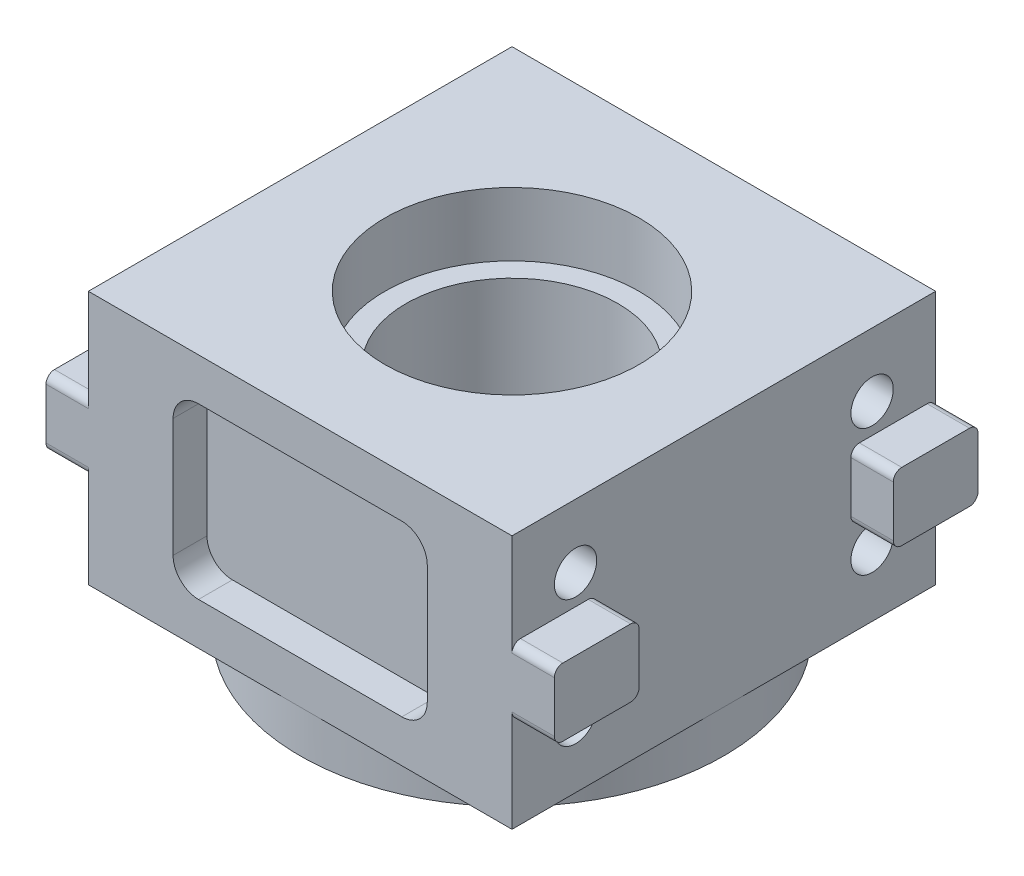
SolidWorks part; units mm, degrees
material "6061-T6 (SS)"
ref_plane "Front Plane" through (0, 0, 0) normal (0, 0, 1) x (1, 0, 0)
ref_plane "Top Plane" through (0, 0, 0) normal (0, 1, 0) x (1, 0, 0)
ref_plane "Right Plane" through (0, 0, 0) normal (1, 0, 0) x (0, 0, -1)
sketch "Sketch1" plane through (0, 0, 0) normal (0, 1, 0) x (1, 0, 0)
  line L1 (63.5, 63.5) -> (-63.5, 63.5)
  line L2 (63.5, 63.5) -> (63.5, -63.5)
  line L3 (63.5, -63.5) -> (-63.5, -63.5)
  line L4 (-63.5, 63.5) -> (-63.5, -63.5)
  line L5 (63.5, 63.5) -> (-63.5, -63.5) construction
  line L6 (63.5, -63.5) -> (-63.5, 63.5) construction
  circle A0 centre (0, 0) radius 38.1
  point P0 (0, 0)
  dimension "D3" = 76.2
  dimension "D1" = 127
  dimension "D2" = 127
extrude "Boss-Extrude1" add sketch "Sketch1" along normal blind 76.2
sketch "Sketch2" plane through (-63.5, 0, 0) normal (-1, 0, 0) x (0, 0, 1)
  line L0 (0, 76.2) -> (0, 0)
  line L1 (-63.5, 76.2) -> (63.5, 76.2) construction
  line L2 (-63.5, 0) -> (63.5, 0) construction
  line L3 (63.5, 76.2) -> (63.5, 0) construction
  line L4 (44.45, 19.05) -> (-44.45, 19.05)
  line L5 (44.45, 19.05) -> (44.45, 57.15)
  line L6 (44.45, 57.15) -> (-44.45, 57.15)
  line L7 (-44.45, 19.05) -> (-44.45, 57.15)
  line L8 (44.45, 19.05) -> (-44.45, 57.15) construction
  line L9 (44.45, 57.15) -> (-44.45, 19.05) construction
  circle A0 centre (-44.45, 57.15) radius 6.35
  circle A1 centre (-44.45, 19.05) radius 6.35
  circle A2 centre (44.45, 57.15) radius 6.35
  circle A3 centre (44.45, 19.05) radius 6.35
  point P6 (0, 38.1)
  dimension "D2" = 12.7
  dimension "D3" = 19.05
  dimension "D4" = 19.05
extrude "Cut-Extrude1" cut sketch "Sketch2" against normal blind 25.4 contours A2 | A0 | A1 | A3
mirror "Mirror1" about plane through (0, 0, 0) normal (1, 0, 0) of "Cut-Extrude1"
sketch "Sketch3" plane through (0, 0, 0) normal (0, -1, 0) x (1, 0, 0)
  circle A0 centre (0, 0) radius 38.1 construction
  circle A1 centre (0, 0) radius 38.1
  circle A2 centre (0, 0) radius 63.5
  dimension "D1" = 127
extrude "Boss-Extrude2" add sketch "Sketch3" along normal blind 12.7
sketch "Sketch4" plane through (0, 0, 63.5) normal (0, 0, 1) x (1, 0, 0)
  line L0 (-63.5, 76.2) -> (-63.5, 0) construction
  line L1 (-63.5, 48.26) -> (-76.2, 48.26)
  line L2 (-63.5, 48.26) -> (-63.5, 27.94)
  line L3 (-63.5, 27.94) -> (-76.2, 27.94)
  line L4 (-76.2, 48.26) -> (-76.2, 27.94)
  line L5 (63.5, 76.2) -> (63.5, 0) construction
  line L6 (63.5, 48.26) -> (76.2, 48.26)
  line L7 (63.5, 48.26) -> (63.5, 27.94)
  line L8 (63.5, 27.94) -> (76.2, 27.94)
  line L9 (76.2, 48.26) -> (76.2, 27.94)
  line L10 (-63.5, 76.2) -> (63.5, 76.2) construction
  line L11 (-63.5, 0) -> (0, 0) construction
  line L12 (0, 0) -> (63.5, 0) construction
  dimension "D1" = 27.94
  dimension "D2" = 27.94
  dimension "D3" = 27.94
  dimension "D4" = 27.94
  dimension "D5" = 12.7
  dimension "D6" = 12.7
extrude "Boss-Extrude3" add sketch "Sketch4" against normal blind 25.4
ref_plane "Plane1" through (0, 0, 0) normal (0, 0, 1) x (1, 0, 0)
fillet "Fillet1" radius 2.54 8 edges at (69.85, 27.94, 63.5) (69.85, 27.94, 38.1) (69.85, 48.26, 38.1) (69.85, 48.26, 63.5) (-69.85, 27.94, 38.1) (-69.85, 48.26, 38.1) (-69.85, 27.94, 63.5) (-69.85, 48.26, 63.5)
mirror "Mirror2" about plane through (0, 0, 0) normal (0, 0, 1) of "Fillet1", "Boss-Extrude3"
sketch "Sketch5" plane through (0, 0, 63.5) normal (0, 0, -1) x (-1, 0, 0)
  line L0 (-63.5, 76.2) -> (63.5, 76.2) construction
  line L1 (-38.1, 63.5) -> (38.1, 63.5)
  line L2 (-38.1, 63.5) -> (-38.1, 12.7)
  line L3 (-38.1, 12.7) -> (38.1, 12.7)
  line L4 (38.1, 63.5) -> (38.1, 12.7)
  line L5 (0, 0) -> (63.5, 0) construction
  line L6 (-63.5, 76.2) -> (-63.5, 45.72) construction
  line L7 (63.5, 76.2) -> (63.5, 45.72) construction
  dimension "D1" = 12.7
  dimension "D2" = 12.7
  dimension "D3" = 25.4
  dimension "D4" = 25.4
extrude "Cut-Extrude3" cut sketch "Sketch5" along normal blind 10.16
fillet "Fillet2" radius 7.62 4 edges at (-38.1, 12.7, 58.42) (38.1, 63.5, 58.42) (38.1, 12.7, 58.42) (-38.1, 63.5, 58.42)
ref_plane "Plane2" through (0, 31.75, 0) normal (0, -1, 0) x (-1, 0, 0)
sketch "Sketch6" plane through (0, 31.75, 0) normal (0, -1, 0) x (-1, 0, 0)
  circle A0 centre (0, 0) radius 38.1
  circle A1 centre (0, 0) radius 31.75
  circle A2 centre (0, 0) radius 38.1 construction
  dimension "D1" = 6.35
extrude "Boss-Extrude4" add sketch "Sketch6" along normal blind 25.4 and the other way blind 25.4
